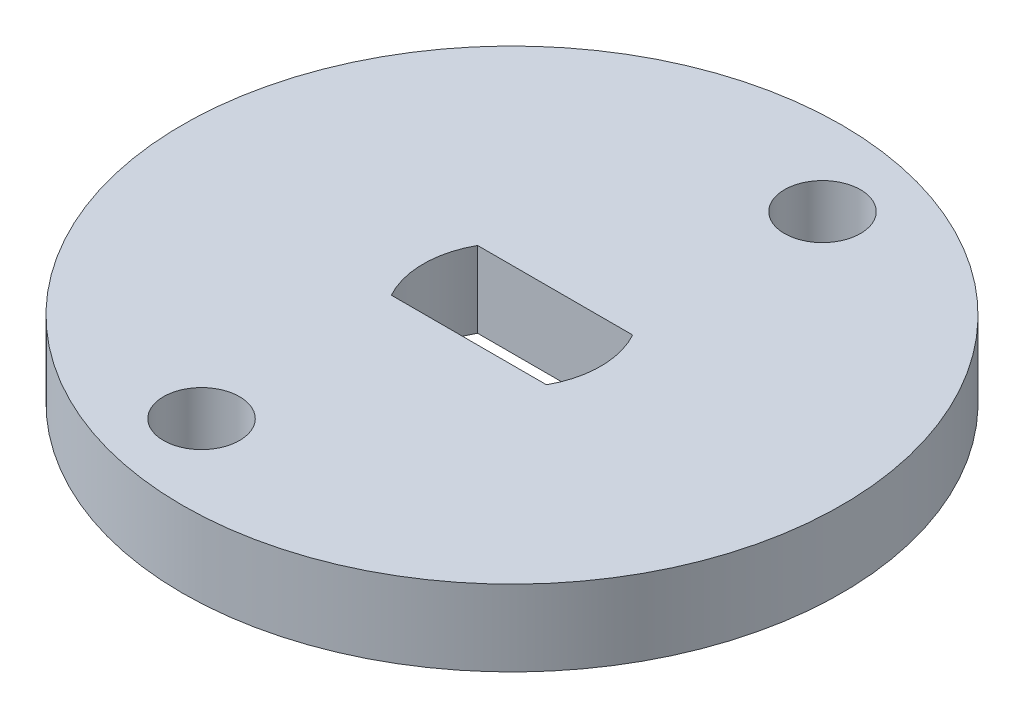
SolidWorks part; units mm, degrees
material "A-Glass Fiber"
ref_plane "Front Plane" through (0, 0, 0) normal (0, 0, 1) x (1, 0, 0)
ref_plane "Top Plane" through (0, 0, 0) normal (0, 1, 0) x (1, 0, 0)
ref_plane "Right Plane" through (0, 0, 0) normal (1, 0, 0) x (0, 0, -1)
sketch "Sketch1" plane through (0, 0, 0) normal (0, 1, 0) x (1, 0, 0)
  line L0 (-3.0594, 1.7) -> (3.0594, 1.7)
  line L1 (3.0594, -1.7) -> (-3.0594, -1.7)
  line L2 (2.5882, 9.6593) -> (-2.5882, -9.6593) construction
  line L3 (0, 0) -> (-8.6387, 0) construction
  arc A0 (-3.0594, 1.7) -> (-3.0594, -1.7) centre (0, 0) ccw
  arc A1 (3.0594, -1.7) -> (3.0594, 1.7) centre (0, 0) ccw
  circle A2 centre (0, 0) radius 13
  circle A3 centre (-2.5882, -9.6593) radius 1.5
  circle A4 centre (2.5882, 9.6593) radius 1.5
  point P9 (0, 0)
  dimension "D1" = 7
  dimension "D3" = 26
  dimension "D5" = 3
  dimension "D2" = 3.4
  dimension "D4" = 20
  dimension "D6" = 75
extrude "Boss-Extrude1" add sketch "Sketch1" along normal blind 3
